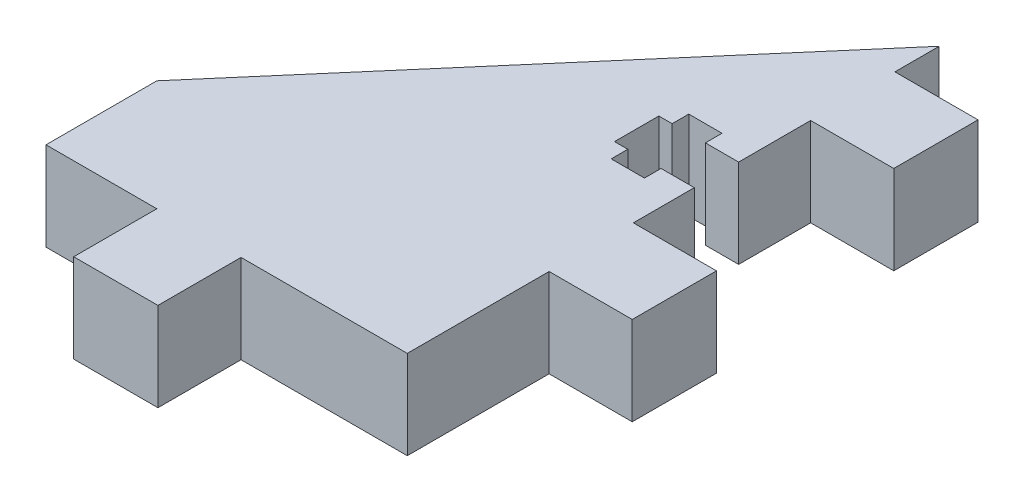
SolidWorks part; units mm, degrees
ref_plane "Front Plane" through (0, 0, 0) normal (0, 0, 1) x (1, 0, 0)
ref_plane "Top Plane" through (0, 0, 0) normal (0, 1, 0) x (1, 0, 0)
ref_plane "Right Plane" through (0, 0, 0) normal (1, 0, 0) x (0, 0, -1)
sketch "Sketch1" plane through (0, 0, 0) normal (0, 1, 0) x (1, 0, 0)
  line L0 (0, 0) -> (-15, 0)
  line L1 (-15, 0) -> (-15, -7.5)
  line L2 (-15, -7.5) -> (-22.6, -7.5)
  line L3 (-22.6, -7.5) -> (-22.6, 0)
  line L4 (-22.6, 0) -> (-32.6, 0)
  line L5 (-32.6, 0) -> (-32.6, 10)
  line L6 (-32.6, 10) -> (0, 48)
  line L7 (0, 48) -> (0, 44)
  line L8 (0, 44) -> (7.5, 44)
  line L9 (7.5, 44) -> (7.5, 36.4)
  line L10 (7.5, 36.4) -> (0, 36.4)
  line L11 (0, 36.4) -> (0, 29.9)
  line L12 (0, 29.9) -> (-3, 29.9)
  line L13 (-3, 29.9) -> (-3, 31.4)
  line L14 (-3, 31.4) -> (-6, 31.4)
  line L15 (-6, 31.4) -> (-6, 29.9)
  line L16 (-6, 29.9) -> (-7.2, 29.9)
  line L17 (-7.2, 29.9) -> (-7.2, 25.9)
  line L18 (-7.2, 25.9) -> (-6, 25.9)
  line L19 (-6, 25.9) -> (-6, 24.4)
  line L20 (-6, 24.4) -> (-3, 24.4)
  line L21 (-3, 24.4) -> (-3, 25.9)
  line L22 (-3, 25.9) -> (0, 25.9)
  line L23 (0, 25.9) -> (0, 20.4)
  line L24 (0, 20.4) -> (7.5, 20.4)
  line L25 (7.5, 20.4) -> (7.5, 12.8)
  line L26 (7.5, 12.8) -> (0, 12.8)
  line L27 (0, 12.8) -> (0, 0)
  line L28 (-3, 29.9) -> (-6, 29.9) construction
  line L29 (-6, 25.9) -> (-3, 25.9) construction
  line L30 (-3, 25.9) -> (-3, 29.9) construction
  line L31 (-6, 29.9) -> (-6, 25.9) construction
  dimension "D1" = 7.6
  dimension "D2" = 7.6
  dimension "D3" = 7.6
  dimension "D4" = 16
  dimension "D5" = 12.8
  dimension "D6" = 15
  dimension "D7" = 10
  dimension "D8" = 10
  dimension "D9" = 4
  dimension "D10" = 7.5
  dimension "D11" = 7.5
  dimension "D12" = 7.5
  dimension "D13" = 4
  dimension "D14" = 3
  dimension "D15" = 3
  dimension "D16" = 1.5
  dimension "D17" = 1.5
  dimension "D18" = 1.2
  dimension "D19" = 5.5
extrude "Boss-Extrude1" add sketch "Sketch1" along normal blind 8
sketch "Sketch2" [suppressed] plane through (0, 8, 0) normal (0, 1, 0) x (1, 0, 0)
  line L0 (0, 29.9) -> (0, 25.9) construction
  line L1 (0, 27.9) -> (-7.2, 27.9) construction
  line L2 (-7.2, 25.9) -> (-7.2, 29.9) construction
  line L3 (7.5, 36.4) -> (7.5, 20.4) construction
  line L4 (0, 36.4) -> (7.5, 36.4) construction
  line L5 (0, 27.9) -> (7.5, 27.9) construction
